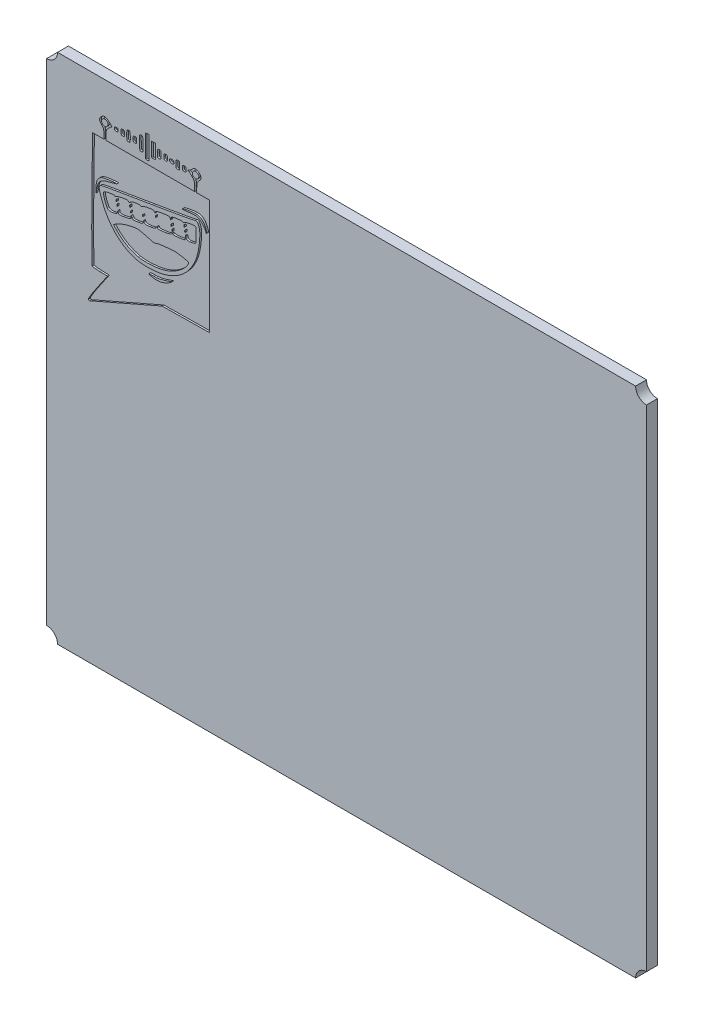
SolidWorks part; units mm, degrees
material "Verre"
ref_plane "Plan de face" through (0, 0, 0) normal (0, 0, 1) x (1, 0, 0)
ref_plane "Plan de dessus" through (0, 0, 0) normal (0, 1, 0) x (1, 0, 0)
ref_plane "Plan de droite" through (0, 0, 0) normal (1, 0, 0) x (0, 0, -1)
sketch "Esquisse1" plane through (0, 0, 0) normal (0, 0, 1) x (1, 0, 0)
  line L1 (0, 0) -> (165, 0)
  line L2 (0, 0) -> (0, 141)
  line L3 (0, 141) -> (165, 141)
  line L4 (165, 0) -> (165, 141)
  dimension "D1" = 165
  dimension "D2" = 141
extrude "Boss.-Extru.1" add sketch "Esquisse1" along normal blind 3
sketch "Esquisse2" plane through (0, 0, 3) normal (0, 0, 1) x (1, 0, 0)
  circle A0 centre (0, 141) radius 3
  circle A1 centre (165, 141) radius 3
  circle A2 centre (165, 0) radius 3
  circle A3 centre (0, 0) radius 3
extrude "Enlèv. mat.-Extru.1" cut sketch "Esquisse2" against normal blind 3
sketch "Esquisse4" plane through (-49.0297, 27.0351, 3) normal (0, 0, 1) x (1, 0, 0)
  line L8 (70.9664, 63.6071) -> (80.7947, 67.9053)
  line L9 (80.7947, 67.9053) -> (87.2814, 68.0036)
  line L10 (87.2814, 68.0036) -> (93.7681, 68.1018)
  line L11 (93.7681, 68.1018) -> (93.8185, 83.8763)
  line L12 (93.8185, 83.8763) -> (93.8688, 99.6508)
  line L13 (93.8688, 99.6508) -> (92.0985, 99.6508)
  line L14 (92.0985, 99.6508) -> (90.3282, 99.6508)
  line L15 (90.3282, 99.6508) -> (90.3282, 100.9134)
  line L16 (89.7385, 100.901) -> (89.7385, 99.6508)
  line L17 (89.7385, 99.6508) -> (77.5514, 99.6508)
  line L18 (77.5514, 99.6508) -> (65.3643, 99.6508)
  line L19 (65.3643, 99.6508) -> (65.3643, 100.901)
  line L20 (64.7746, 100.9134) -> (64.7746, 99.6508)
  line L21 (64.7746, 99.6508) -> (63.2341, 99.6508)
  line L22 (63.2341, 99.6508) -> (61.6935, 99.6508)
  line L23 (61.6935, 99.6508) -> (61.5635, 91.2476)
  line L24 (63.7637, 67.5686) -> (65.7855, 67.5122)
  line L25 (65.7855, 67.5122) -> (63.1036, 63.6122)
  line L32 (68.3128, 79.6906) -> (67.4282, 80.6038)
  line L33 (67.4282, 80.6038) -> (67.9196, 80.9815)
  line L34 (87.2044, 87.5671) -> (87.0849, 86.7861)
  line L35 (87.0849, 86.7861) -> (85.6225, 86.542)
  line L36 (72.5285, 84.7863) -> (72.2441, 85.1924)
  line L37 (72.2441, 85.1924) -> (72.2441, 84.7592)
  line L38 (62.6369, 87.0292) -> (62.6614, 85.7929)
  line L39 (62.6614, 85.7929) -> (62.8069, 86.7833)
  line L150 (77.1583, 103.7787) -> (77.1583, 106.9238)
  line L151 (77.1583, 106.9238) -> (76.6668, 106.9238)
  line L152 (76.6668, 106.9238) -> (76.1754, 106.9238)
  line L153 (76.1754, 106.9238) -> (76.1754, 103.7787)
  line L154 (76.1754, 103.7787) -> (76.1754, 100.6336)
  line L155 (76.1754, 100.6336) -> (76.6668, 100.6336)
  line L156 (76.6668, 100.6336) -> (77.1583, 100.6336)
  line L157 (77.1583, 100.6336) -> (77.1583, 103.7787)
  line L158 (78.9274, 103.7787) -> (78.9274, 105.7444)
  line L159 (78.9274, 105.7444) -> (78.4359, 105.7444)
  line L160 (78.4359, 105.7444) -> (77.9445, 105.7444)
  line L161 (77.9445, 105.7444) -> (77.9445, 103.7787)
  line L162 (77.9445, 103.7787) -> (77.9445, 101.813)
  line L163 (77.9445, 101.813) -> (78.4359, 101.813)
  line L164 (78.4359, 101.813) -> (78.9274, 101.813)
  line L165 (78.9274, 101.813) -> (78.9274, 103.7787)
  spline S0 degree 3 poles (90.3282, 100.9134) (90.3282, 102.0541) (90.3851, 102.2328) (90.9179, 102.7656) knots 0 0 0 0 1 1 1 1
  spline S1 degree 3 poles (90.9179, 102.7656) (91.6338, 103.4815) (91.6648, 104.0325) (91.0252, 104.6722) knots 0 0 0 0 1 1 1 1
  spline S2 degree 3 poles (91.0252, 104.6722) (90.3662, 105.3312) (89.6326, 105.2932) (88.9523, 104.565) knots 0 0 0 0 1 1 1 1
  spline S3 degree 3 poles (88.9523, 104.565) (88.6493, 104.2406) (88.3042, 103.9753) (88.1854, 103.9753) knots 0 0 0 0 1 1 1 1
  spline S4 degree 3 poles (88.1854, 103.9753) (88.0666, 103.9753) (87.9694, 103.8868) (87.9694, 103.7787) knots 0 0 0 0 1 1 1 1
  spline S5 degree 3 poles (87.9694, 103.7787) (87.9694, 103.6706) (88.0638, 103.5821) (88.1792, 103.5821) knots 0 0 0 0 1 1 1 1
  spline S6 degree 3 poles (88.1792, 103.5821) (88.2946, 103.5821) (88.6926, 103.2602) (89.0638, 102.8667) knots 0 0 0 0 1 1 1 1
  spline S7 degree 3 poles (89.0638, 102.8667) (89.6867, 102.2062) (89.7385, 102.0551) (89.7385, 100.901) knots 0 0 0 0 1 1 1 1
  spline S8 degree 3 poles (65.3643, 100.901) (65.3643, 102.0551) (65.4161, 102.2062) (66.0391, 102.8667) knots 0 0 0 0 1 1 1 1
  spline S9 degree 3 poles (66.0391, 102.8667) (66.4102, 103.2602) (66.8189, 103.5821) (66.9473, 103.5821) knots 0 0 0 0 1 1 1 1
  spline S10 degree 3 poles (66.9473, 103.5821) (67.0757, 103.5821) (66.8162, 103.936) (66.3706, 104.3684) knots 0 0 0 0 1 1 1 1
  spline S11 degree 3 poles (66.3706, 104.3684) (65.4216, 105.2893) (64.7798, 105.3744) (64.0777, 104.6722) knots 0 0 0 0 1 1 1 1
  spline S12 degree 3 poles (64.0777, 104.6722) (63.438, 104.0326) (63.469, 103.4815) (64.1849, 102.7656) knots 0 0 0 0 1 1 1 1
  spline S13 degree 3 poles (64.1849, 102.7656) (64.7177, 102.2328) (64.7746, 102.0541) (64.7746, 100.9134) knots 0 0 0 0 1 1 1 1
  spline S14 degree 3 poles (61.5635, 91.2476) (61.3896, 80.0135) (61.4033, 68.158) (61.5905, 67.8635) knots 0 0 0 0 1 1 1 1
  spline S15 degree 3 poles (61.5905, 67.8635) (61.6889, 67.7085) (62.4494, 67.6054) (63.7637, 67.5686) knots 0 0 0 0 1 1 1 1
  spline S16 degree 3 poles (63.1036, 63.6122) (61.4407, 61.194) (60.4651, 59.5992) (60.5359, 59.4147) knots 0 0 0 0 1 1 1 1
  spline S17 degree 3 poles (60.5359, 59.4147) (60.5987, 59.2511) (60.7598, 59.1604) (60.8941, 59.2131) knots 0 0 0 0 1 1 1 1
  spline S18 degree 3 poles (60.8941, 59.2131) (61.0283, 59.2658) (65.5609, 61.2431) (70.9664, 63.6071) knots 0 0 0 0 1 1 1 1
  spline S27 degree 3 poles (81.0048, 73.6026) (81.5379, 73.7631) (82.3722, 74.1707) (82.8587, 74.5085) knots 0 0 0 0 1 1 1 1
  spline S28 degree 3 poles (82.8587, 74.5085) (83.3452, 74.8462) (83.5663, 75.0576) (83.3501, 74.9781) knots 0 0 0 0 1 1 1 1
  spline S29 degree 3 poles (83.3501, 74.9781) (81.0777, 74.1435) (79.8767, 73.871) (78.4359, 73.863) knots 0 0 0 0 1 1 1 1
  spline S30 degree 3 poles (78.4359, 73.863) (76.9176, 73.8545) (76.8871, 73.8455) (77.5514, 73.5975) knots 0 0 0 0 1 1 1 1
  spline S31 degree 3 poles (77.5514, 73.5975) (78.4851, 73.2491) (79.8367, 73.2511) (81.0048, 73.6026) knots 0 0 0 0 1 1 1 1
  spline S32 degree 3 poles (81.146, 75.6529) (85.6434, 76.8209) (88.8091, 79.7858) (90.2982, 84.2247) knots 0 0 0 0 1 1 1 1
  spline S33 degree 3 poles (90.2982, 84.2247) (90.9209, 86.0806) (91.3519, 89.6853) (91.1192, 91.0909) knots 0 0 0 0 1 1 1 1
  spline S34 degree 3 poles (91.1192, 91.0909) (90.893, 92.4577) (90.3893, 93.1167) (89.8135, 92.7992) knots 0 0 0 0 1 1 1 1
  spline S35 degree 3 poles (89.8135, 92.7992) (89.6101, 92.687) (84.5787, 91.7835) (78.6325, 90.7914) knots 0 0 0 0 1 1 1 1
  spline S36 degree 3 poles (78.6325, 90.7914) (63.3308, 88.2382) (63.964, 88.3583) (63.6664, 87.9514) knots 0 0 0 0 1 1 1 1
  spline S37 degree 3 poles (63.6664, 87.9514) (63.3829, 87.5636) (63.4346, 87.2118) (64.0415, 85.3997) knots 0 0 0 0 1 1 1 1
  spline S38 degree 3 poles (64.0415, 85.3997) (65.8335, 80.0497) (69.587, 76.3218) (74.139, 75.3713) knots 0 0 0 0 1 1 1 1
  spline S39 degree 3 poles (74.139, 75.3713) (75.9109, 75.0013) (79.136, 75.1309) (81.146, 75.6529) knots 0 0 0 0 1 1 1 1
  spline S40 degree 3 poles (74.308, 76.3393) (71.8844, 76.8993) (69.9915, 77.9575) (68.3128, 79.6906) knots 0 0 0 0 1 1 1 1
  spline S41 degree 3 poles (67.9196, 80.9815) (68.6596, 81.5502) (70.6737, 82.3093) (72.3742, 82.6606) knots 0 0 0 0 1 1 1 1
  spline S42 degree 3 poles (72.3742, 82.6606) (73.7445, 82.9437) (74.0317, 82.9448) (75.3764, 82.673) knots 0 0 0 0 1 1 1 1
  spline S43 degree 3 poles (75.3764, 82.673) (76.1943, 82.5076) (77.2417, 82.2384) (77.7041, 82.0747) knots 0 0 0 0 1 1 1 1
  spline S44 degree 3 poles (77.7041, 82.0747) (78.3493, 81.8462) (78.6692, 81.8265) (79.08, 81.9899) knots 0 0 0 0 1 1 1 1
  spline S45 degree 3 poles (79.08, 81.9899) (79.3745, 82.107) (79.8807, 82.237) (80.205, 82.2788) knots 0 0 0 0 1 1 1 1
  spline S46 degree 3 poles (80.205, 82.2788) (83.1547, 82.6592) (83.978, 82.7231) (84.7819, 82.6343) knots 0 0 0 0 1 1 1 1
  spline S47 degree 3 poles (84.7819, 82.6343) (86.3439, 82.4617) (87.975, 82.1098) (88.0922, 81.9202) knots 0 0 0 0 1 1 1 1
  spline S48 degree 3 poles (88.0922, 81.9202) (88.1534, 81.8212) (87.957, 81.3846) (87.6559, 80.95) knots 0 0 0 0 1 1 1 1
  spline S49 degree 3 poles (87.6559, 80.95) (86.327, 79.0324) (83.7169, 77.3534) (80.9521, 76.6377) knots 0 0 0 0 1 1 1 1
  spline S50 degree 3 poles (80.9521, 76.6377) (78.9519, 76.1199) (75.8587, 75.981) (74.308, 76.3393) knots 0 0 0 0 1 1 1 1
  spline S51 degree 3 poles (65.6837, 83.7781) (65.1048, 84.695) (64.5011, 86.7081) (64.7071, 87.0347) knots 0 0 0 0 1 1 1 1
  spline S52 degree 3 poles (64.7071, 87.0347) (64.9509, 87.4213) (67.5225, 87.9394) (67.8033, 87.6586) knots 0 0 0 0 1 1 1 1
  spline S53 degree 3 poles (67.8033, 87.6586) (67.925, 87.5369) (68.1029, 87.5653) (68.3002, 87.7378) knots 0 0 0 0 1 1 1 1
  spline S54 degree 3 poles (68.3002, 87.7378) (68.4693, 87.8856) (69.2237, 88.1114) (69.9766, 88.2396) knots 0 0 0 0 1 1 1 1
  spline S55 degree 3 poles (69.9766, 88.2396) (71.149, 88.4392) (71.3765, 88.4306) (71.5601, 88.1794) knots 0 0 0 0 1 1 1 1
  spline S56 degree 3 poles (71.5601, 88.1794) (71.747, 87.9238) (71.8032, 87.9318) (71.9965, 88.2413) knots 0 0 0 0 1 1 1 1
  spline S57 degree 3 poles (71.9965, 88.2413) (72.2619, 88.6662) (74.5717, 89.146) (74.8779, 88.8398) knots 0 0 0 0 1 1 1 1
  spline S58 degree 3 poles (74.8779, 88.8398) (75.002, 88.7157) (75.1784, 88.7471) (75.3798, 88.9295) knots 0 0 0 0 1 1 1 1
  spline S59 degree 3 poles (75.3798, 88.9295) (75.5507, 89.0841) (76.3058, 89.3089) (77.0579, 89.429) knots 0 0 0 0 1 1 1 1
  spline S60 degree 3 poles (77.0579, 89.429) (78.2565, 89.6205) (78.4543, 89.608) (78.6593, 89.3277) knots 0 0 0 0 1 1 1 1
  spline S61 degree 3 poles (78.6593, 89.3277) (78.8725, 89.0361) (78.8991, 89.0392) (78.9613, 89.3623) knots 0 0 0 0 1 1 1 1
  spline S62 degree 3 poles (78.9613, 89.3623) (79.0151, 89.6414) (79.4053, 89.7862) (80.7967, 90.0433) knots 0 0 0 0 1 1 1 1
  spline S63 degree 3 poles (80.7967, 90.0433) (82.6214, 90.3804) (83.0306, 90.3101) (83.0785, 89.651) knots 0 0 0 0 1 1 1 1
  spline S64 degree 3 poles (83.0785, 89.651) (83.0913, 89.475) (83.1581, 89.5938) (83.2269, 89.9149) knots 0 0 0 0 1 1 1 1
  spline S65 degree 3 poles (83.2269, 89.9149) (83.3456, 90.4691) (83.4266, 90.5112) (84.821, 90.7447) knots 0 0 0 0 1 1 1 1
  spline S66 degree 3 poles (84.821, 90.7447) (85.7574, 90.9015) (86.3584, 90.9224) (86.4784, 90.8024) knots 0 0 0 0 1 1 1 1
  spline S67 degree 3 poles (86.4784, 90.8024) (86.5984, 90.6824) (86.7782, 90.7114) (86.9741, 90.8823) knots 0 0 0 0 1 1 1 1
  spline S68 degree 3 poles (86.9741, 90.8823) (87.4067, 91.2598) (89.7627, 91.646) (90.026, 91.3826) knots 0 0 0 0 1 1 1 1
  spline S69 degree 3 poles (90.026, 91.3826) (90.2682, 91.1403) (90.2358, 87.6857) (89.989, 87.4389) knots 0 0 0 0 1 1 1 1
  spline S70 degree 3 poles (89.989, 87.4389) (89.8964, 87.3463) (89.3822, 87.1887) (88.8464, 87.0886) knots 0 0 0 0 1 1 1 1
  spline S71 degree 3 poles (88.8464, 87.0886) (87.7287, 86.8797) (87.3943, 87.0461) (87.3518, 87.8317) knots 0 0 0 0 1 1 1 1
  spline S72 degree 3 poles (87.3518, 87.8317) (87.3327, 88.1865) (87.2865, 88.1037) (87.2044, 87.5671) knots 0 0 0 0 1 1 1 1
  spline S73 degree 3 poles (85.6225, 86.542) (84.5457, 86.3623) (84.0906, 86.3557) (83.8964, 86.5169) knots 0 0 0 0 1 1 1 1
  spline S74 degree 3 poles (83.8964, 86.5169) (83.6981, 86.6814) (83.5732, 86.6603) (83.3931, 86.4319) knots 0 0 0 0 1 1 1 1
  spline S75 degree 3 poles (83.3931, 86.4319) (83.2613, 86.2648) (82.5713, 86.0305) (81.8597, 85.9113) knots 0 0 0 0 1 1 1 1
  spline S76 degree 3 poles (81.8597, 85.9113) (80.0022, 85.6001) (79.5176, 85.6264) (79.5141, 86.0386) knots 0 0 0 0 1 1 1 1
  spline S77 degree 3 poles (79.5141, 86.0386) (79.5124, 86.2918) (79.4461, 86.2539) (79.2645, 85.895) knots 0 0 0 0 1 1 1 1
  spline S78 degree 3 poles (79.2645, 85.895) (79.0588, 85.4883) (78.7902, 85.3696) (77.6458, 85.1794) knots 0 0 0 0 1 1 1 1
  spline S79 degree 3 poles (77.6458, 85.1794) (76.2116, 84.9411) (75.8043, 85.0469) (75.759, 85.6695) knots 0 0 0 0 1 1 1 1
  spline S80 degree 3 poles (75.759, 85.6695) (75.7462, 85.8455) (75.6793, 85.726) (75.6104, 85.404) knots 0 0 0 0 1 1 1 1
  spline S81 degree 3 poles (75.6104, 85.404) (75.4926, 84.8538) (75.4047, 84.8054) (74.149, 84.5994) knots 0 0 0 0 1 1 1 1
  spline S82 degree 3 poles (74.149, 84.5994) (72.8907, 84.393) (72.7963, 84.4039) (72.5285, 84.7863) knots 0 0 0 0 1 1 1 1
  spline S83 degree 3 poles (72.2441, 84.7592) (72.2441, 84.3022) (72.2712, 84.3135) (70.2321, 83.9199) knots 0 0 0 0 1 1 1 1
  spline S84 degree 3 poles (70.2321, 83.9199) (68.9732, 83.6768) (68.7164, 83.753) (68.6826, 84.3794) knots 0 0 0 0 1 1 1 1
  spline S85 degree 3 poles (68.6826, 84.3794) (68.6654, 84.6987) (68.6268, 84.658) (68.5335, 84.222) knots 0 0 0 0 1 1 1 1
  spline S86 degree 3 poles (68.5335, 84.222) (68.4371, 83.7713) (68.2703, 83.6045) (67.8197, 83.5081) knots 0 0 0 0 1 1 1 1
  spline S87 degree 3 poles (67.8197, 83.5081) (66.5753, 83.2419) (65.9743, 83.3178) (65.6837, 83.7781) knots 0 0 0 0 1 1 1 1
  spline S88 degree 3 poles (68.4429, 85.9403) (68.3884, 86.0754) (68.3438, 85.9648) (68.3438, 85.6946) knots 0 0 0 0 1 1 1 1
  spline S89 degree 3 poles (68.3438, 85.6946) (68.3438, 85.4243) (68.3884, 85.3137) (68.4429, 85.4489) knots 0 0 0 0 1 1 1 1
  spline S90 degree 3 poles (68.4429, 85.4489) (68.4975, 85.584) (68.4975, 85.8051) (68.4429, 85.9403) knots 0 0 0 0 1 1 1 1
  spline S91 degree 3 poles (72.1818, 86.1246) (72.1191, 86.2814) (72.0725, 86.2348) (72.0631, 86.0058) knots 0 0 0 0 1 1 1 1
  spline S92 degree 3 poles (72.0631, 86.0058) (72.0545, 85.7986) (72.101, 85.6825) (72.1663, 85.7478) knots 0 0 0 0 1 1 1 1
  spline S93 degree 3 poles (72.1663, 85.7478) (72.2316, 85.8131) (72.2386, 85.9827) (72.1818, 86.1246) knots 0 0 0 0 1 1 1 1
  spline S94 degree 3 poles (68.2504, 86.9108) (68.1877, 87.0676) (68.1411, 87.0211) (68.1317, 86.7921) knots 0 0 0 0 1 1 1 1
  spline S95 degree 3 poles (68.1317, 86.7921) (68.1231, 86.5849) (68.1696, 86.4687) (68.235, 86.5341) knots 0 0 0 0 1 1 1 1
  spline S96 degree 3 poles (68.235, 86.5341) (68.3003, 86.5994) (68.3073, 86.7689) (68.2504, 86.9108) knots 0 0 0 0 1 1 1 1
  spline S97 degree 3 poles (75.5234, 86.9108) (75.4607, 87.0676) (75.4141, 87.0211) (75.4047, 86.7921) knots 0 0 0 0 1 1 1 1
  spline S98 degree 3 poles (75.4047, 86.7921) (75.3961, 86.5849) (75.4426, 86.4687) (75.5079, 86.5341) knots 0 0 0 0 1 1 1 1
  spline S99 degree 3 poles (75.5079, 86.5341) (75.5732, 86.5994) (75.5802, 86.7689) (75.5234, 86.9108) knots 0 0 0 0 1 1 1 1
  spline S100 degree 3 poles (71.9811, 87.5128) (71.9266, 87.648) (71.882, 87.5374) (71.882, 87.2671) knots 0 0 0 0 1 1 1 1
  spline S101 degree 3 poles (71.882, 87.2671) (71.882, 86.9968) (71.9266, 86.8863) (71.9811, 87.0214) knots 0 0 0 0 1 1 1 1
  spline S102 degree 3 poles (71.9811, 87.0214) (72.0357, 87.1565) (72.0357, 87.3777) (71.9811, 87.5128) knots 0 0 0 0 1 1 1 1
  spline S103 degree 3 poles (83.5786, 87.5128) (83.524, 87.648) (83.4794, 87.5374) (83.4794, 87.2671) knots 0 0 0 0 1 1 1 1
  spline S104 degree 3 poles (83.4794, 87.2671) (83.4794, 86.9968) (83.524, 86.8863) (83.5786, 87.0214) knots 0 0 0 0 1 1 1 1
  spline S105 degree 3 poles (83.5786, 87.0214) (83.6331, 87.1565) (83.6331, 87.3777) (83.5786, 87.5128) knots 0 0 0 0 1 1 1 1
  spline S106 degree 3 poles (79.0616, 88.4834) (78.9989, 88.6402) (78.9523, 88.5936) (78.9429, 88.3646) knots 0 0 0 0 1 1 1 1
  spline S107 degree 3 poles (78.9429, 88.3646) (78.9343, 88.1574) (78.9808, 88.0413) (79.0461, 88.1066) knots 0 0 0 0 1 1 1 1
  spline S108 degree 3 poles (79.0461, 88.1066) (79.1114, 88.1719) (79.1184, 88.3415) (79.0616, 88.4834) knots 0 0 0 0 1 1 1 1
  spline S109 degree 3 poles (83.382, 88.6922) (83.3275, 88.8274) (83.2829, 88.7168) (83.2829, 88.4465) knots 0 0 0 0 1 1 1 1
  spline S110 degree 3 poles (83.2829, 88.4465) (83.2829, 88.1762) (83.3275, 88.0657) (83.382, 88.2008) knots 0 0 0 0 1 1 1 1
  spline S111 degree 3 poles (83.382, 88.2008) (83.4366, 88.3359) (83.4366, 88.5571) (83.382, 88.6922) knots 0 0 0 0 1 1 1 1
  spline S112 degree 3 poles (87.1168, 89.0853) (87.0622, 89.2205) (87.0176, 89.1099) (87.0176, 88.8396) knots 0 0 0 0 1 1 1 1
  spline S113 degree 3 poles (87.0176, 88.8396) (87.0176, 88.5694) (87.0622, 88.4588) (87.1168, 88.5939) knots 0 0 0 0 1 1 1 1
  spline S114 degree 3 poles (87.1168, 88.5939) (87.1713, 88.7291) (87.1713, 88.9502) (87.1168, 89.0853) knots 0 0 0 0 1 1 1 1
  spline S115 degree 3 poles (86.9202, 90.2647) (86.8657, 90.3999) (86.8211, 90.2893) (86.8211, 90.019) knots 0 0 0 0 1 1 1 1
  spline S116 degree 3 poles (86.8211, 90.019) (86.8211, 89.7488) (86.8657, 89.6382) (86.9202, 89.7733) knots 0 0 0 0 1 1 1 1
  spline S117 degree 3 poles (86.9202, 89.7733) (86.9748, 89.9085) (86.9748, 90.1296) (86.9202, 90.2647) knots 0 0 0 0 1 1 1 1
  spline S118 degree 3 poles (63.2698, 88.3876) (63.7691, 89.353) (64.4336, 89.7416) (66.3922, 90.2132) knots 0 0 0 0 1 1 1 1
  spline S119 degree 3 poles (66.3922, 90.2132) (67.3944, 90.4545) (68.2587, 90.6978) (68.3128, 90.7538) knots 0 0 0 0 1 1 1 1
  spline S120 degree 3 poles (68.3128, 90.7538) (68.5606, 91.0108) (64.9774, 90.5376) (64.2464, 90.2168) knots 0 0 0 0 1 1 1 1
  spline S121 degree 3 poles (64.2464, 90.2168) (63.1193, 89.7221) (62.6037, 88.701) (62.6369, 87.0292) knots 0 0 0 0 1 1 1 1
  spline S122 degree 3 poles (62.8069, 86.7833) (62.8869, 87.328) (63.0952, 88.05) (63.2698, 88.3876) knots 0 0 0 0 1 1 1 1
  spline S123 degree 3 poles (92.687, 92.6727) (92.0126, 94.0659) (91.3078, 94.5401) (89.9113, 94.5401) knots 0 0 0 0 1 1 1 1
  spline S124 degree 3 poles (89.9113, 94.5401) (88.6905, 94.5401) (85.8345, 93.9229) (86.4585, 93.7939) knots 0 0 0 0 1 1 1 1
  spline S125 degree 3 poles (86.4585, 93.7939) (86.6545, 93.7533) (87.5573, 93.819) (88.4648, 93.9398) knots 0 0 0 0 1 1 1 1
  spline S126 degree 3 poles (88.4648, 93.9398) (89.8134, 94.1192) (90.2355, 94.1088) (90.7767, 93.8827) knots 0 0 0 0 1 1 1 1
  spline S127 degree 3 poles (90.7767, 93.8827) (91.523, 93.5709) (92.6332, 92.3333) (92.8321, 91.5916) knots 0 0 0 0 1 1 1 1
  spline S128 degree 3 poles (92.8321, 91.5916) (92.9345, 91.2096) (92.9802, 91.1778) (93.0373, 91.4488) knots 0 0 0 0 1 1 1 1
  spline S129 degree 3 poles (93.0373, 91.4488) (93.0777, 91.6405) (92.9201, 92.1913) (92.687, 92.6727) knots 0 0 0 0 1 1 1 1
  spline S130 degree 3 poles (64.5288, 103.0082) (63.8291, 103.4157) (64.2282, 104.565) (65.0694, 104.565) knots 0 0 0 0 1 1 1 1
  spline S131 degree 3 poles (65.0694, 104.565) (65.8972, 104.565) (66.2388, 103.6985) (65.6451, 103.1048) knots 0 0 0 0 1 1 1 1
  spline S132 degree 3 poles (65.6451, 103.1048) (65.2897, 102.7494) (65.0141, 102.7256) (64.5288, 103.0082) knots 0 0 0 0 1 1 1 1
  spline S133 degree 3 poles (89.4928, 103.0082) (88.7931, 103.4157) (89.1922, 104.565) (90.0334, 104.565) knots 0 0 0 0 1 1 1 1
  spline S134 degree 3 poles (90.0334, 104.565) (90.8611, 104.565) (91.2027, 103.6985) (90.609, 103.1048) knots 0 0 0 0 1 1 1 1
  spline S135 degree 3 poles (90.609, 103.1048) (90.2537, 102.7494) (89.9781, 102.7256) (89.4928, 103.0082) knots 0 0 0 0 1 1 1 1
  spline S238 degree 3 poles (75.5857, 103.6866) (75.5857, 105.1706) (75.5244, 105.5837) (75.2909, 105.6733) knots 0 0 0 0 1 1 1 1
  spline S239 degree 3 poles (75.2909, 105.6733) (74.6082, 105.9352) (74.5029, 105.649) (74.5672, 103.7059) knots 0 0 0 0 1 1 1 1
  spline S240 degree 3 poles (74.5672, 103.7059) (74.6287, 101.8493) (74.639, 101.813) (75.1078, 101.813) knots 0 0 0 0 1 1 1 1
  spline S241 degree 3 poles (75.1078, 101.813) (75.5806, 101.813) (75.5857, 101.8333) (75.5857, 103.6866) knots 0 0 0 0 1 1 1 1
  spline S242 degree 3 poles (72.0475, 103.7787) (72.0475, 105.1154) (72.0335, 105.1547) (71.5561, 105.1547) knots 0 0 0 0 1 1 1 1
  spline S243 degree 3 poles (71.5561, 105.1547) (71.0787, 105.1547) (71.0647, 105.1154) (71.0647, 103.7787) knots 0 0 0 0 1 1 1 1
  spline S244 degree 3 poles (71.0647, 103.7787) (71.0647, 102.4421) (71.0787, 102.4027) (71.5561, 102.4027) knots 0 0 0 0 1 1 1 1
  spline S245 degree 3 poles (71.5561, 102.4027) (72.0335, 102.4027) (72.0475, 102.4421) (72.0475, 103.7787) knots 0 0 0 0 1 1 1 1
  spline S246 degree 3 poles (80.4999, 103.6804) (80.4999, 104.7026) (80.4731, 104.7615) (80.0085, 104.7615) knots 0 0 0 0 1 1 1 1
  spline S247 degree 3 poles (80.0085, 104.7615) (79.5439, 104.7615) (79.5171, 104.7026) (79.5171, 103.6804) knots 0 0 0 0 1 1 1 1
  spline S248 degree 3 poles (79.5171, 103.6804) (79.5171, 102.6583) (79.5438, 102.5993) (80.0085, 102.5993) knots 0 0 0 0 1 1 1 1
  spline S249 degree 3 poles (80.0085, 102.5993) (80.4731, 102.5993) (80.4999, 102.6583) (80.4999, 103.6804) knots 0 0 0 0 1 1 1 1
  spline S250 degree 3 poles (85.6106, 103.6804) (85.6106, 104.7026) (85.5839, 104.7615) (85.1192, 104.7615) knots 0 0 0 0 1 1 1 1
  spline S251 degree 3 poles (85.1192, 104.7615) (84.6546, 104.7615) (84.6278, 104.7026) (84.6278, 103.6804) knots 0 0 0 0 1 1 1 1
  spline S252 degree 3 poles (84.6278, 103.6804) (84.6278, 102.6583) (84.6546, 102.5993) (85.1192, 102.5993) knots 0 0 0 0 1 1 1 1
  spline S253 degree 3 poles (85.1192, 102.5993) (85.5838, 102.5993) (85.6106, 102.6583) (85.6106, 103.6804) knots 0 0 0 0 1 1 1 1
  spline S254 degree 3 poles (70.475, 103.7787) (70.475, 104.4863) (70.4259, 104.565) (69.9836, 104.565) knots 0 0 0 0 1 1 1 1
  spline S255 degree 3 poles (69.9836, 104.565) (69.5413, 104.565) (69.4922, 104.4863) (69.4922, 103.7787) knots 0 0 0 0 1 1 1 1
  spline S256 degree 3 poles (69.4922, 103.7787) (69.4922, 103.0711) (69.5413, 102.9924) (69.9836, 102.9924) knots 0 0 0 0 1 1 1 1
  spline S257 degree 3 poles (69.9836, 102.9924) (70.4258, 102.9924) (70.475, 103.0711) (70.475, 103.7787) knots 0 0 0 0 1 1 1 1
  spline S258 degree 3 poles (73.8166, 103.7787) (73.8166, 104.4863) (73.7675, 104.565) (73.3252, 104.565) knots 0 0 0 0 1 1 1 1
  spline S259 degree 3 poles (73.3252, 104.565) (72.8829, 104.565) (72.8338, 104.4863) (72.8338, 103.7787) knots 0 0 0 0 1 1 1 1
  spline S260 degree 3 poles (72.8338, 103.7787) (72.8338, 103.0711) (72.8829, 102.9924) (73.3252, 102.9924) knots 0 0 0 0 1 1 1 1
  spline S261 degree 3 poles (73.3252, 102.9924) (73.7675, 102.9924) (73.8166, 103.0711) (73.8166, 103.7787) knots 0 0 0 0 1 1 1 1
  spline S262 degree 3 poles (82.269, 103.7787) (82.269, 104.4863) (82.2198, 104.565) (81.7776, 104.565) knots 0 0 0 0 1 1 1 1
  spline S263 degree 3 poles (81.7776, 104.565) (81.3353, 104.565) (81.2862, 104.4863) (81.2862, 103.7787) knots 0 0 0 0 1 1 1 1
  spline S264 degree 3 poles (81.2862, 103.7787) (81.2862, 103.0711) (81.3353, 102.9924) (81.7776, 102.9924) knots 0 0 0 0 1 1 1 1
  spline S265 degree 3 poles (81.7776, 102.9924) (82.2198, 102.9924) (82.269, 103.0711) (82.269, 103.7787) knots 0 0 0 0 1 1 1 1
  spline S266 degree 3 poles (87.3797, 103.6804) (87.3797, 104.2832) (87.3189, 104.3684) (86.8883, 104.3684) knots 0 0 0 0 1 1 1 1
  spline S267 degree 3 poles (86.8883, 104.3684) (86.4577, 104.3684) (86.3969, 104.2832) (86.3969, 103.6804) knots 0 0 0 0 1 1 1 1
  spline S268 degree 3 poles (86.3969, 103.6804) (86.3969, 103.0776) (86.4578, 102.9924) (86.8883, 102.9924) knots 0 0 0 0 1 1 1 1
  spline S269 degree 3 poles (86.8883, 102.9924) (87.3189, 102.9924) (87.3797, 103.0776) (87.3797, 103.6804) knots 0 0 0 0 1 1 1 1
  spline S270 degree 3 poles (68.7059, 103.6804) (68.7059, 104.0736) (68.6076, 104.1718) (68.2145, 104.1718) knots 0 0 0 0 1 1 1 1
  spline S271 degree 3 poles (68.2145, 104.1718) (67.8213, 104.1718) (67.7231, 104.0736) (67.7231, 103.6804) knots 0 0 0 0 1 1 1 1
  spline S272 degree 3 poles (67.7231, 103.6804) (67.7231, 103.2873) (67.8213, 103.189) (68.2145, 103.189) knots 0 0 0 0 1 1 1 1
  spline S273 degree 3 poles (68.2145, 103.189) (68.6076, 103.189) (68.7059, 103.2873) (68.7059, 103.6804) knots 0 0 0 0 1 1 1 1
  spline S274 degree 3 poles (84.0381, 103.6804) (84.0381, 104.0954) (83.9464, 104.1718) (83.4484, 104.1718) knots 0 0 0 0 1 1 1 1
  spline S275 degree 3 poles (83.4484, 104.1718) (83.0076, 104.1718) (82.8587, 104.0808) (82.8587, 103.8115) knots 0 0 0 0 1 1 1 1
  spline S276 degree 3 poles (82.8587, 103.8115) (82.8587, 103.3341) (83.0267, 103.189) (83.5794, 103.189) knots 0 0 0 0 1 1 1 1
  spline S277 degree 3 poles (83.5794, 103.189) (83.9376, 103.189) (84.0381, 103.2967) (84.0381, 103.6804) knots 0 0 0 0 1 1 1 1
extrude "Enlèv. mat.-Extru.2" cut sketch "Esquisse4" against normal blind 0.5 contours S17 S18 L8 L9 L10 L11 L12 L13 L14 L15 S0 S1 S2 S3 S4 S5 S6 S7 L16 L17 L18 L19 S8 S9 S10 S11 S12 S13 L20 L21 L22 L23 S14 S15 L24 L25 S16 S129 S128 S127 S126 S125 S124 S123 S122 L39 L38 S121 S120 | S87 S86 S85 S84 S83 L37 L36 S82 S81 S80 S79 S78 S77 S76 S75 S74 S73 L35 L34 S72 S71 S70 S69 S68 S67 S66 S65 S64 S63 S62 S61 S60 S59 S58 S57 S56 S55 S54 S53 S52 S51 S117 S116 S115 S114 S113 S112 S111 | S272 S273 S270 S271 | S256 S257 S254 S255 | S244 S245 S242 S243 | S260 S261 S258 S259 | S240 S241 S238 S239 | L156 L157 L150 L151 L152 L153 L154 L155 | L164 L165 L158 L159 L160 L161 L162 L163 | S248 S249 S246 S247 | S264 S265 S262 S263 | S276 S277 S274 S275 | S252 S253 S250 S251 | S268 S269 S266 S267 | S50 S49 S48 S47 S46 S45 S44 S43 S42 S41 L33 L32 S40 | L39 S122 S118 S119 S120 S121 L38
